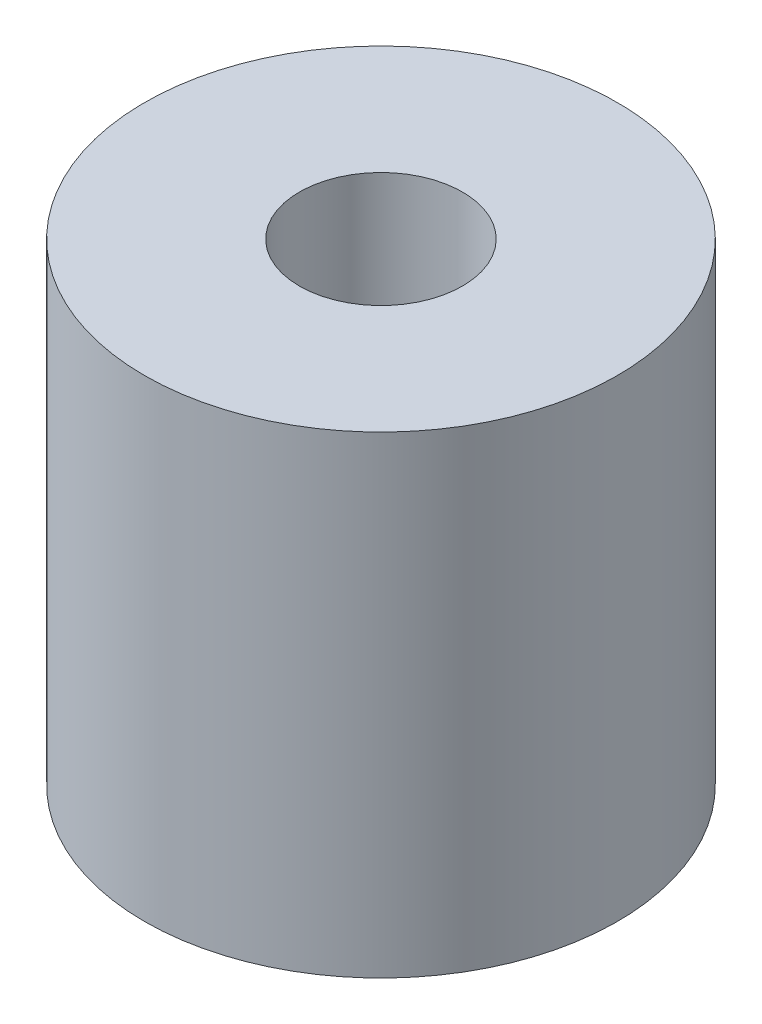
SolidWorks part; units mm, degrees
ref_plane "Front Plane" through (0, 0, 0) normal (0, 0, 1) x (1, 0, 0)
ref_plane "Top Plane" through (0, 0, 0) normal (0, 1, 0) x (1, 0, 0)
ref_plane "Right Plane" through (0, 0, 0) normal (1, 0, 0) x (0, 0, -1)
sketch "Sketch1" plane through (0, 0, 0) normal (0, 1, 0) x (1, 0, 0)
  circle A0 centre (0, 0) radius 29
  circle A1 centre (0, 0) radius 10
  dimension "D1" = 58
  dimension "D2" = 20
extrude "Boss-Extrude1" add sketch "Sketch1" along normal blind 58
